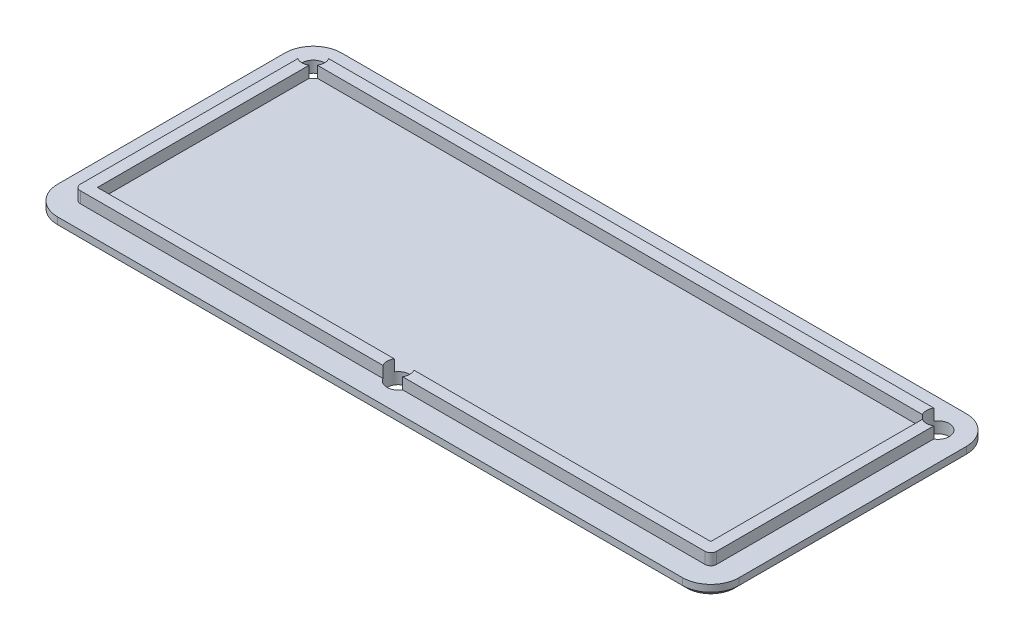
SolidWorks part; units mm, degrees
ref_plane "Plane XZ" through (0, 0, 0) normal (0, 0, 1) x (1, 0, 0)
ref_plane "Plane XY" through (0, 0, 0) normal (0, 1, 0) x (1, 0, 0)
ref_plane "Plane YZ" through (0, 0, 0) normal (1, 0, 0) x (0, 0, -1)
sketch "Sketch1" plane through (0, 0, 0) normal (0, 1, 0) x (1, 0, 0)
  line L0 (0, 15.875) -> (0, -15.875) construction
  line L1 (-38.1, 15.875) -> (38.1, 15.875)
  line L2 (-38.1, 15.875) -> (-38.1, -15.875)
  line L3 (-38.1, -15.875) -> (38.1, -15.875)
  line L4 (38.1, 15.875) -> (38.1, -15.875)
  dimension "D1" = 76.2
  dimension "D2" = 31.75
extrude "Boss-Extrude1" add sketch "Sketch1" along normal blind 1.27
fillet "Fillet1" radius 3.175 4 edges at (-38.1, 0.635, -15.875) (38.1, 0.635, -15.875) (38.1, 0.635, 15.875) (-38.1, 0.635, 15.875)
sketch "Sketch2" plane through (0, 1.27, 0) normal (0, 1, 0) x (1, 0, 0)
  line L4 (34.29, 12.065) -> (-34.29, 12.065)
  line L5 (-34.29, 12.065) -> (-34.29, -12.065)
  line L6 (-34.29, -12.065) -> (34.29, -12.065)
  line L7 (34.29, -12.065) -> (34.29, 12.065)
  line L8 (34.925, 13.335) -> (-34.925, 13.335)
  line L9 (-35.56, 12.7) -> (-35.56, -12.7)
  line L10 (-34.925, -13.335) -> (34.925, -13.335)
  line L11 (35.56, -12.7) -> (35.56, 12.7)
  line L12 (34.925, 13.335) -> (-34.925, 13.335)
  line L13 (-35.56, 12.7) -> (-35.56, -12.7)
  line L14 (-34.925, -13.335) -> (34.925, -13.335)
  line L15 (35.56, -12.7) -> (35.56, 12.7)
  arc A4 (-34.29, 12.065) -> (-34.29, 12.065) centre (-34.29, 12.065) ccw
  arc A5 (-34.29, -12.065) -> (-34.29, -12.065) centre (-34.29, -12.065) ccw
  arc A6 (34.29, -12.065) -> (34.29, -12.065) centre (34.29, -12.065) ccw
  arc A7 (34.29, 12.065) -> (34.29, 12.065) centre (34.29, 12.065) ccw
  arc A8 (-34.925, 13.335) -> (-35.56, 12.7) centre (-34.925, 12.7) ccw
  arc A9 (-35.56, -12.7) -> (-34.925, -13.335) centre (-34.925, -12.7) ccw
  arc A10 (34.925, -13.335) -> (35.56, -12.7) centre (34.925, -12.7) ccw
  arc A11 (35.56, 12.7) -> (34.925, 13.335) centre (34.925, 12.7) ccw
  arc A12 (-34.925, 13.335) -> (-35.56, 12.7) centre (-34.925, 12.7) ccw
  arc A13 (-35.56, -12.7) -> (-34.925, -13.335) centre (-34.925, -12.7) ccw
  arc A14 (34.925, -13.335) -> (35.56, -12.7) centre (34.925, -12.7) ccw
  arc A15 (35.56, 12.7) -> (34.925, 13.335) centre (34.925, 12.7) ccw
  dimension "D1" = 2.54
  dimension "D2" = 1.27
extrude "Boss-Extrude2" add sketch "Sketch2" along normal blind 1.27
sketch "Sketch3" plane through (0, 0, 0) normal (0, -1, 0) x (1, 0, 0)
  line L0 (-34.925, 15.875) -> (34.925, 15.875) construction
  line L1 (0, 0) -> (0, 12.7) construction
  circle A0 centre (34.925, -12.7) radius 3.175 construction
  circle A1 centre (0, 12.7) radius 3.175 construction
  circle A2 centre (-34.925, -12.7) radius 3.175 construction
  arc A3 (34.925, -15.875) -> (38.1, -12.7) centre (34.925, -12.7) ccw construction
  arc A4 (-38.1, -12.7) -> (-34.925, -15.875) centre (-34.925, -12.7) ccw construction
  circle A5 centre (34.925, -12.7) radius 1.27
  circle A6 centre (0, 12.7) radius 1.27
  circle A7 centre (-34.925, -12.7) radius 1.27
  dimension "D1" = 6.35
  dimension "D2" = 2.54
extrude "Cut-Extrude1" cut sketch "Sketch3" against normal through all
chamfer "Chamfer1" distance 0.508 angle 45 8 edges at (0, 0, -15.875) (-37.1701, 0, -14.9451) (37.1701, 0, -14.9451) (-38.1, 0, 0) (38.1, 0, 0) (-37.1701, 0, 14.9451) (37.1701, 0, 14.9451) (0, 0, 15.875)
